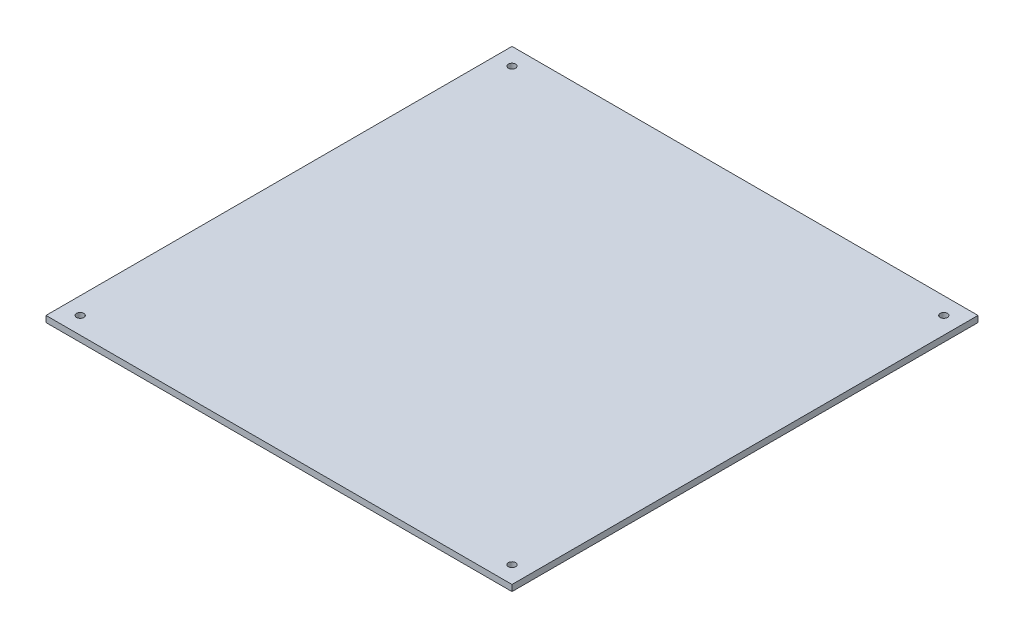
SolidWorks part; units mm, degrees
ref_plane "Front Plane" through (0, 0, 0) normal (0, 0, 1) x (1, 0, 0)
ref_plane "Top Plane" through (0, 0, 0) normal (0, 1, 0) x (1, 0, 0)
ref_plane "Right Plane" through (0, 0, 0) normal (1, 0, 0) x (0, 0, -1)
sketch "Sketch1" plane through (0, 0, 0) normal (0, 1, 0) x (1, 0, 0)
  line L1 (0, 0) -> (225, 0)
  line L2 (0, 0) -> (0, 225)
  line L3 (0, 225) -> (225, 225)
  line L4 (225, 0) -> (225, 225)
  line L5 (0, 0) -> (225, 225) construction
  line L6 (0, 225) -> (225, 0) construction
  point P4 (112.5, 112.5)
  dimension "D1" = 225
  dimension "D2" = 225
extrude "Boss-Extrude1" add sketch "Sketch1" along normal blind 3
sketch "Sketch2" plane through (0, 3, 0) normal (0, 1, 0) x (1, 0, 0)
  line L0 (222.5, 222.5) -> (222.5, 225) construction
  line L1 (2.5, 2.5) -> (222.5, 2.5) construction
  line L2 (2.5, 2.5) -> (2.5, 222.5) construction
  line L3 (2.5, 222.5) -> (222.5, 222.5) construction
  line L4 (222.5, 2.5) -> (222.5, 222.5) construction
  line L5 (112.5, 222.5) -> (112.5, 2.5) construction
  line L6 (2.5, 112.5) -> (222.5, 112.5) construction
  line L7 (225, 225) -> (0, 225) construction
  line L8 (222.5, 222.5) -> (225, 222.5) construction
  line L9 (225, 0) -> (225, 225) construction
  line L10 (2.5, 2.5) -> (0, 2.5) construction
  line L11 (0, 225) -> (0, 0) construction
  line L12 (2.5, 2.5) -> (2.5, 0) construction
  line L13 (0, 0) -> (225, 0) construction
  circle A0 centre (216.74, 216.74) radius 1.75
  circle A1 centre (8.26, 216.74) radius 1.75
  circle A2 centre (216.74, 8.26) radius 1.75
  circle A3 centre (8.26, 8.26) radius 1.75
  dimension "D2" = 5.76
  dimension "D4" = 3.5
  dimension "D1" = 220
  dimension "D3" = 5.76
extrude "Cut-Extrude1" cut sketch "Sketch2" against normal through all
